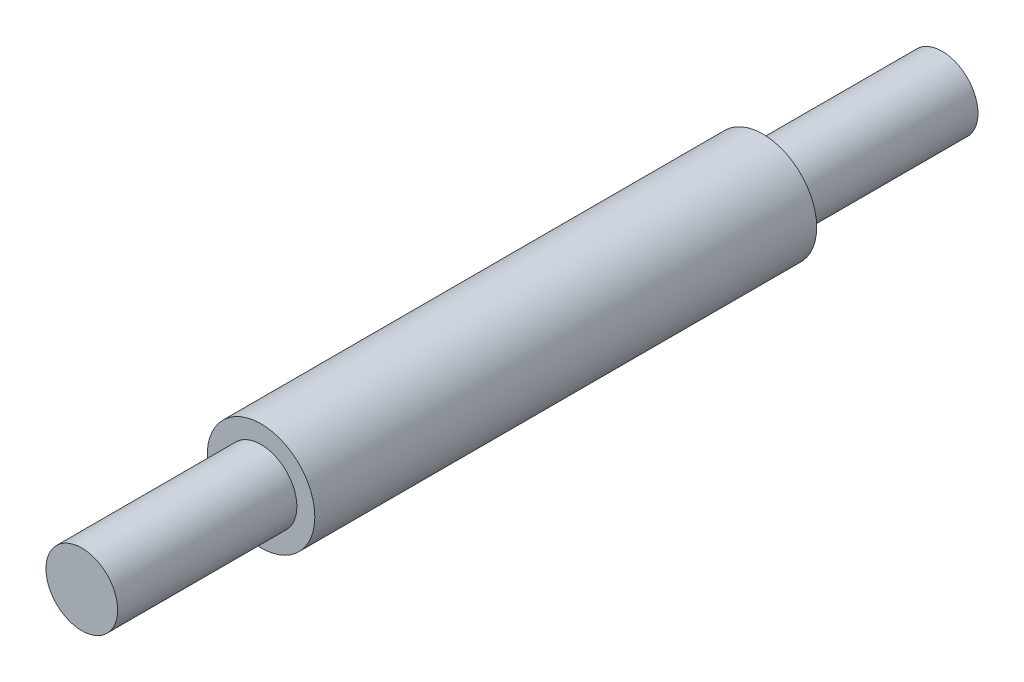
SolidWorks part; units mm, degrees
material "Plain Carbon Steel"
ref_plane "Front Plane" through (0, 0, 0) normal (0, 0, 1) x (1, 0, 0)
ref_plane "Top Plane" through (0, 0, 0) normal (0, 1, 0) x (1, 0, 0)
ref_plane "Right Plane" through (0, 0, 0) normal (1, 0, 0) x (0, 0, -1)
sketch "Sketch1" plane through (0, 0, 0) normal (0, 0, 1) x (1, 0, 0)
  circle A0 centre (0, 0) radius 19.05
  dimension "D1" = 38.1
extrude "Boss-Extrude1" add sketch "Sketch1" along normal blind 177.8
sketch "Sketch2" plane through (0, 0, 177.8) normal (0, 0, 1) x (1, 0, 0)
  circle A0 centre (0, 0) radius 12.7
  dimension "D1" = 25.4
extrude "Boss-Extrude2" add sketch "Sketch2" along normal blind 63.5
sketch "Sketch3" plane through (0, 0, 0) normal (0, 0, -1) x (-1, 0, 0)
  circle A0 centre (0, 0) radius 12.7
  dimension "D1" = 25.4
extrude "Boss-Extrude3" add sketch "Sketch3" along normal blind 63.5
